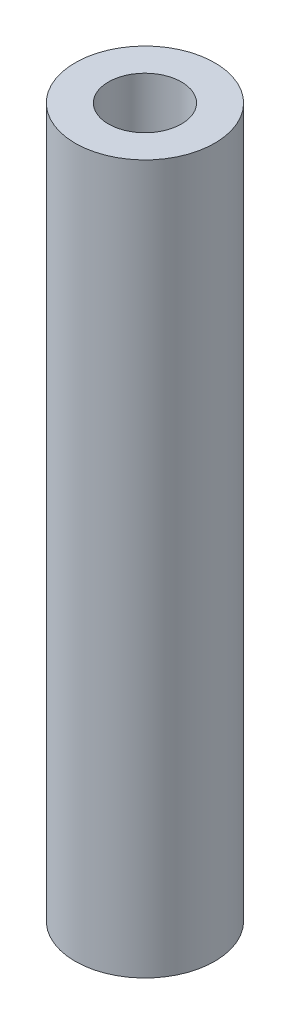
SolidWorks part; units mm, degrees
ref_plane "Front Plane" through (0, 0, 0) normal (0, 0, 1) x (1, 0, 0)
ref_plane "Top Plane" through (0, 0, 0) normal (0, 1, 0) x (1, 0, 0)
ref_plane "Right Plane" through (0, 0, 0) normal (1, 0, 0) x (0, 0, -1)
sketch "Sketch1" plane through (0, 0, 0) normal (0, 1, 0) x (1, 0, 0)
  circle A0 centre (0, 0) radius 1.7
  circle A1 centre (0, 0) radius 3.25
  dimension "D1" = 3.4
  dimension "D2" = 6.5
extrude "Boss-Extrude1" add sketch "Sketch1" along normal blind 33
